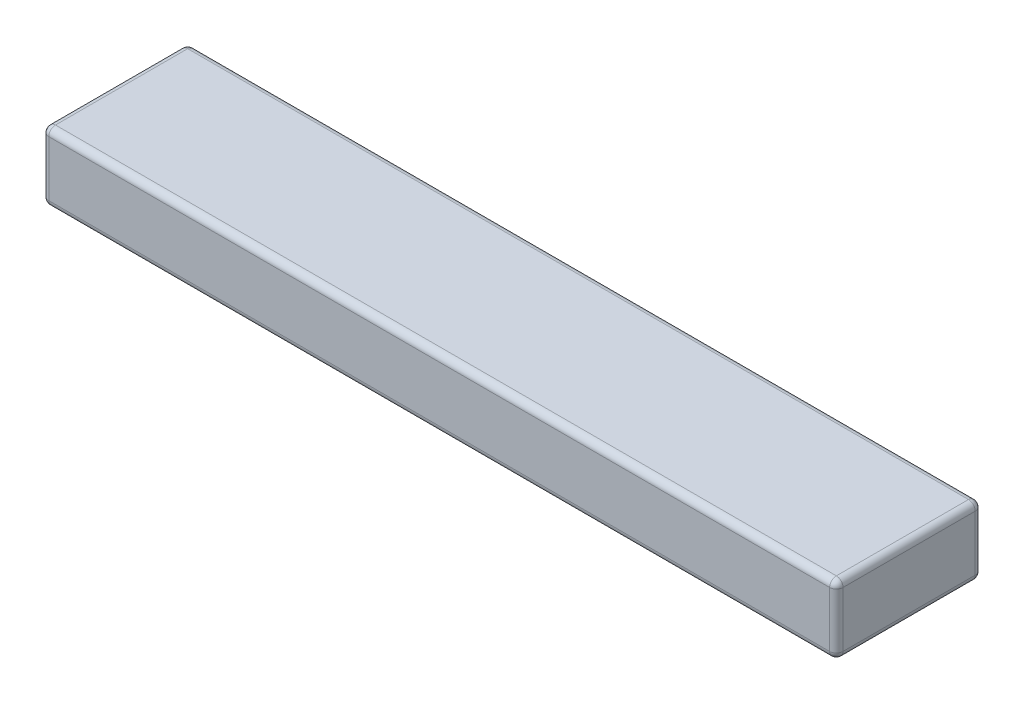
SolidWorks part; units mm, degrees
ref_plane "Front Plane" through (0, 0, 0) normal (0, 0, 1) x (1, 0, 0)
ref_plane "Top Plane" through (0, 0, 0) normal (0, 1, 0) x (1, 0, 0)
ref_plane "Right Plane" through (0, 0, 0) normal (1, 0, 0) x (0, 0, -1)
sketch "Sketch1" plane through (0, 0, 0) normal (0, 1, 0) x (1, 0, 0)
  line L1 (150, -27.5) -> (-150, -27.5)
  line L2 (150, -27.5) -> (150, 27.5)
  line L3 (150, 27.5) -> (-150, 27.5)
  line L4 (-150, -27.5) -> (-150, 27.5)
  line L5 (150, -27.5) -> (-150, 27.5) construction
  line L6 (150, 27.5) -> (-150, -27.5) construction
  point P0 (0, 0)
  dimension "D1" = 300
  dimension "D2" = 55
extrude "Boss-Extrude1" add sketch "Sketch1" along normal blind 26
fillet "Fillet1" radius 2.54 12 edges at (-150, 0, 0) (-150, 13, -27.5) (0, 0, -27.5) (150, 13, -27.5) (150, 0, 0) (-150, 13, 27.5) (150, 13, 27.5) (0, 0, 27.5) (0, 26, -27.5) (150, 26, 0) (0, 26, 27.5) (-150, 26, 0)
